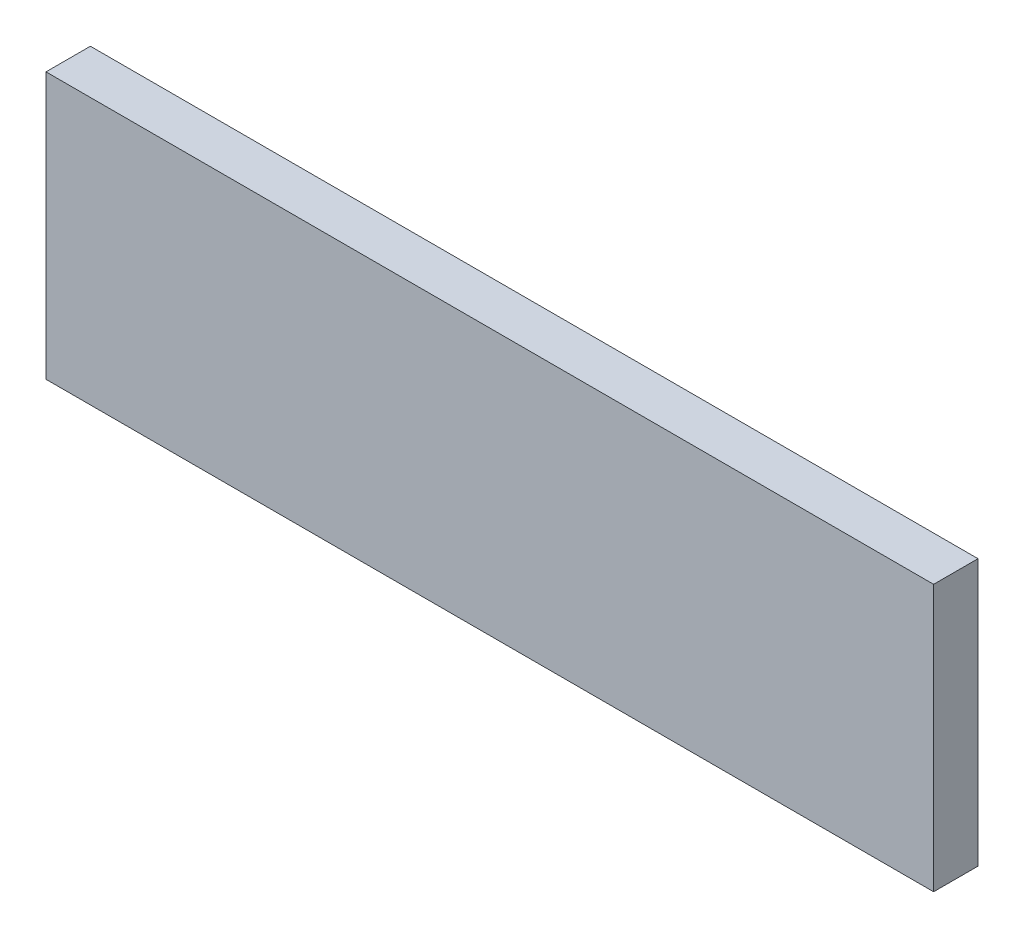
SolidWorks part; units mm, degrees
ref_plane "Front Plane" through (0, 0, 0) normal (0, 0, 1) x (1, 0, 0)
ref_plane "Top Plane" through (0, 0, 0) normal (0, 1, 0) x (1, 0, 0)
ref_plane "Right Plane" through (0, 0, 0) normal (1, 0, 0) x (0, 0, -1)
sketch "Sketch1" plane through (0, 0, 0) normal (0, 0, 1) x (1, 0, 0)
  line L1 (0, 0) -> (-2000, 0)
  line L2 (0, 0) -> (0, -600)
  line L3 (0, -600) -> (-2000, -600)
  line L4 (-2000, 0) -> (-2000, -600)
  dimension "D1" = 600
  dimension "D2" = 2000
extrude "Boss-Extrude1" add sketch "Sketch1" along normal blind 100
